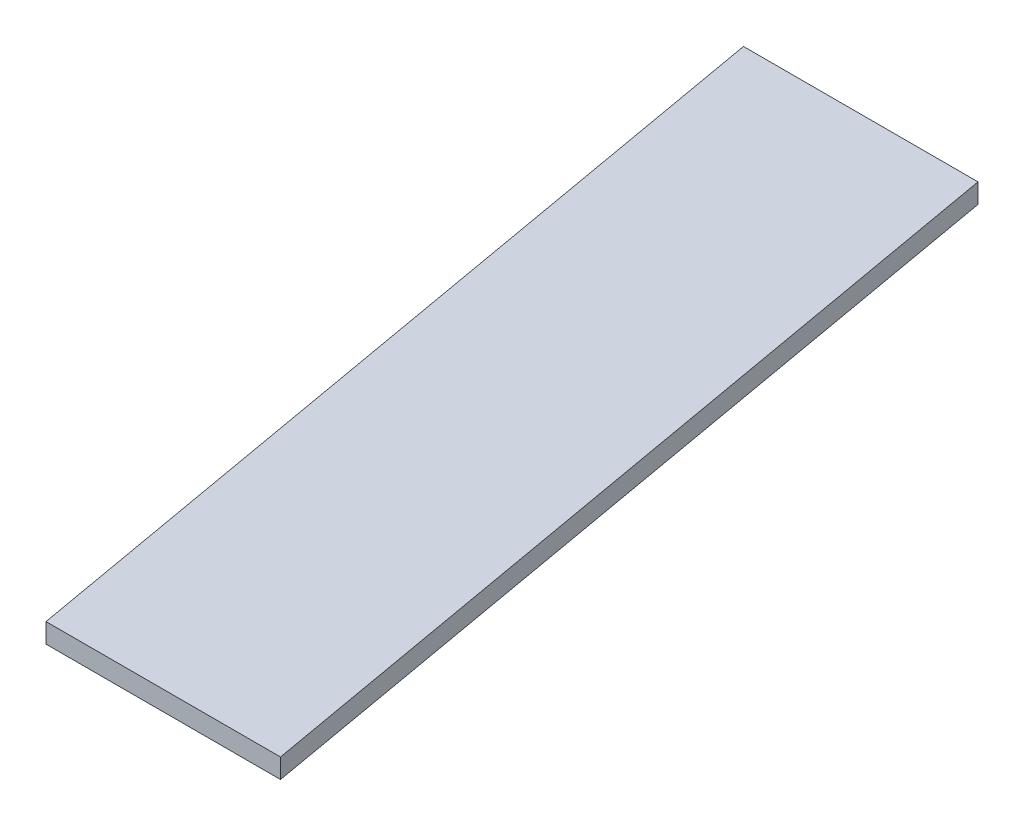
SolidWorks part; units mm, degrees
material "Balsa"
ref_plane "Front Plane" through (0, 0, 0) normal (0, 0, 1) x (1, 0, 0)
ref_plane "Top Plane" through (0, 0, 0) normal (0, 1, 0) x (1, 0, 0)
ref_plane "Right Plane" through (0, 0, 0) normal (1, 0, 0) x (0, 0, -1)
sketch "Sketch1" plane through (0, 0, 0) normal (0, 1, 0) x (1, 0, 0)
  line L0 (0, 0) -> (-24.2587, 137.5776)
  line L1 (-24.2587, 137.5776) -> (13.8413, 137.5776)
  line L2 (13.8413, 137.5776) -> (38.1, 0)
  line L3 (38.1, 0) -> (0, 0)
  dimension "D1" = 139.7
  dimension "D2" = 38.1
  dimension "D3" = 100
extrude "Boss-Extrude1" add sketch "Sketch1" along normal blind 3.175
